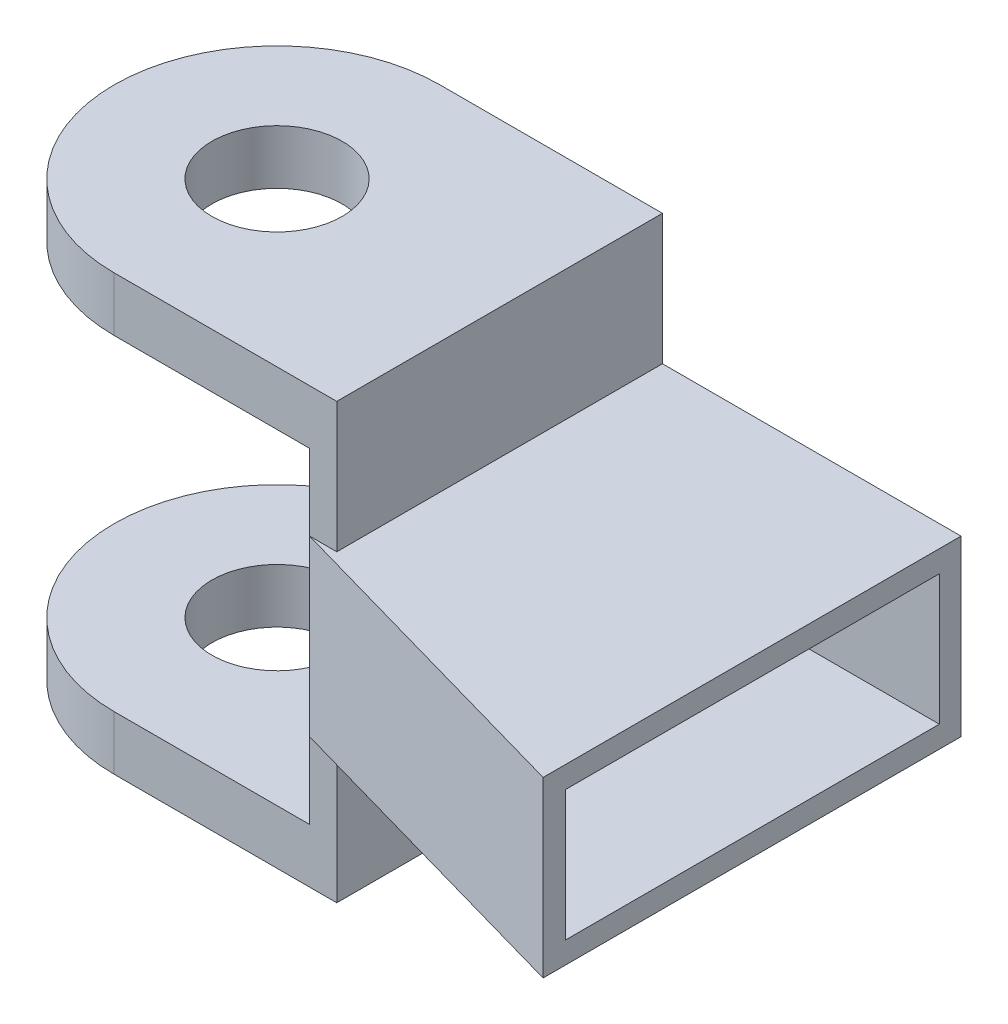
SolidWorks part; units mm, degrees
ref_plane "Front" through (0, 0, 0) normal (0, 0, 1) x (1, 0, 0)
ref_plane "Top" through (0, 0, 0) normal (0, 1, 0) x (1, 0, 0)
ref_plane "Right" through (0, 0, 0) normal (1, 0, 0) x (0, 0, -1)
sketch "Sketch1" plane through (0, 0, 0) normal (0, 1, 0) x (1, 0, 0)
  line L0 (-350, 31.0082) -> (-320, 22.5144)
  line L4 (-350, 31.0082) -> (-350, 61.0082)
  line L5 (-350, 61.0082) -> (-320, 61.0082)
  line L10 (-320, 61.0082) -> (-320, 22.5144)
  dimension "D4" = 30
  dimension "D6" = 30
extrude "Boss-Extrude1" add sketch "Sketch1" along normal blind 16
shell "Shell1" thickness 2
ref_plane "Plane1" through (0, 8, 0) normal (0, -1, 0) x (-1, 0, 0)
ref_plane "Plane2" through (0, 23, 0) normal (0, 1, 0) x (1, 0, 0)
sketch "Sketch2" plane through (0, 23, 0) normal (0, 1, 0) x (1, 0, 0)
  line L0 (-350, 61.0082) -> (-368, 61.0082)
  line L1 (-350, 31.0082) -> (-368, 31.0082)
  line L3 (-350, 61.0082) -> (-350, 31.0082)
  arc A0 (-368, 61.0082) -> (-368, 31.0082) centre (-368, 46.0082) ccw
  circle A1 centre (-368, 46.0082) radius 6
  dimension "D4" = 12
  dimension "D1" = 15
  dimension "D2" = 18
  dimension "D3" = 18
extrude "Boss-Extrude2" add sketch "Sketch2" along normal blind 5 separate body
sketch "Sketch4" plane through (-350, 0, 0) normal (-1, 0, 0) x (0, 0, 1)
  line L5 (-61.0082, 16) -> (-61.0082, 28)
  line L6 (-61.0082, 28) -> (-31.0082, 28)
  line L7 (-31.0082, 28) -> (-61.0082, 28) construction
  line L8 (-31.0082, 28) -> (-31.0082, 16)
  line L9 (-31.0082, 16) -> (-61.0082, 16)
extrude "Boss-Extrude3" add sketch "Sketch4" against normal blind 2.5
mirror "Mirror14" about plane through (0, 8, 0) normal (0, -1, 0) of "Boss-Extrude3"
sketch "Sketch5" plane through (0, -12, 0) normal (0, -1, 0) x (1, 0, 0)
  line L0 (-350, -31.0082) -> (-368, -31.0082)
  line L1 (-350, -31.0082) -> (-350, -61.0082)
  line L2 (-350, -61.0082) -> (-368, -61.0082)
  arc A0 (-368, -31.0082) -> (-362.4291, -59.9354) centre (-368, -46.0082) ccw
  arc A1 (-368, -31.0082) -> (-368, -61.0082) centre (-368, -46.0082) ccw construction
  circle A2 centre (-368, -46.0082) radius 6
  line M1 (-350, -31.0082) -> (-350, -61.0082)
extrude "Boss-Extrude4" add sketch "Sketch5" against normal blind 5 contours L0 A0 L2 A2 M1
